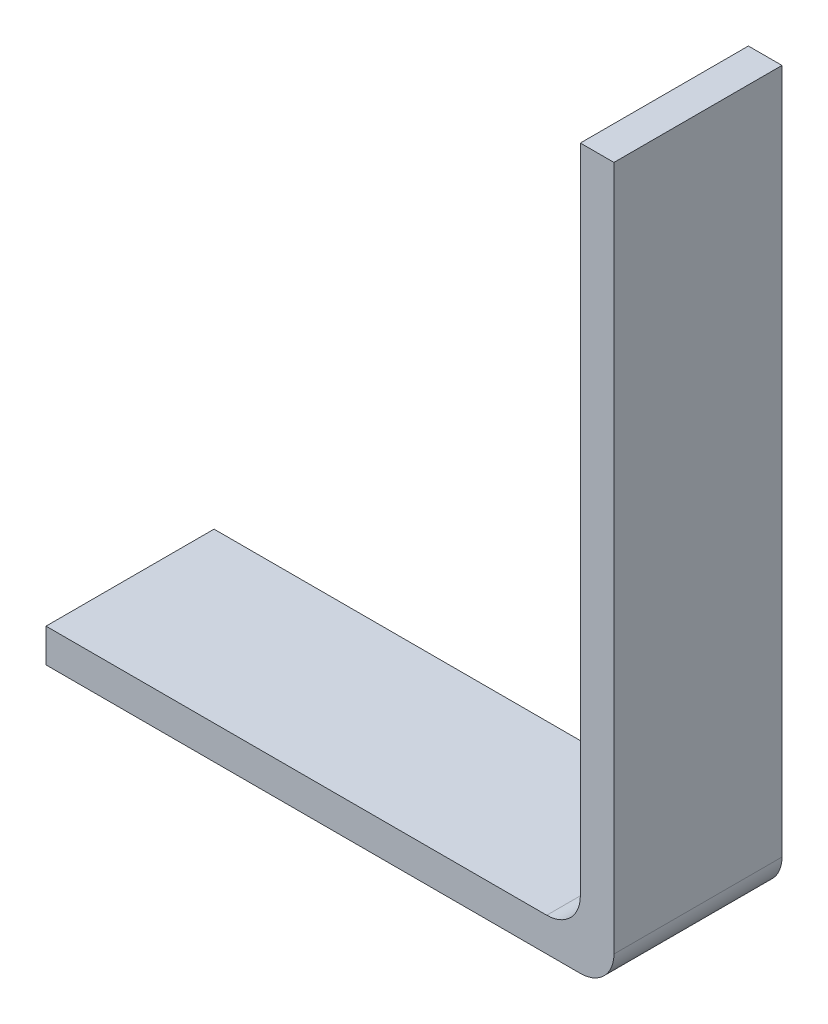
SolidWorks part; units mm, degrees
ref_plane "Front Plane" through (0, 0, 0) normal (0, 0, 1) x (1, 0, 0)
ref_plane "Top Plane" through (0, 0, 0) normal (0, 1, 0) x (1, 0, 0)
ref_plane "Right Plane" through (0, 0, 0) normal (1, 0, 0) x (0, 0, -1)
sketch "Sketch1" plane through (0, 0, 0) normal (0, 0, 1) x (1, 0, 0)
  line L0 (0, 0) -> (15.9, 0)
  line L1 (15.9, 0) -> (15.9, 20.4)
  dimension "D1" = 20.4
  dimension "D2" = 15.9
extrude "Extrude-Thin1" add sketch "Sketch1" along normal blind 5 thin
fillet "Fillet1" radius 1 2 edges at (15.9, 0, 2.5) (16.9, -1, 2.5)
